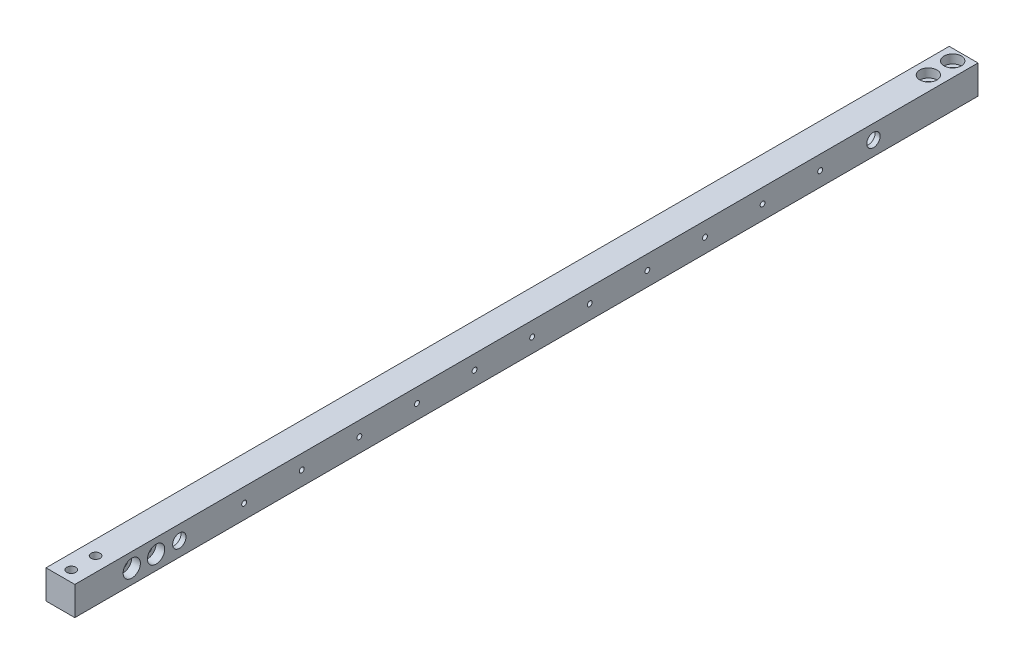
SolidWorks part; units mm, degrees
ref_plane "Front Plane" through (0, 0, 0) normal (0, 0, 1) x (1, 0, 0)
ref_plane "Top Plane" through (0, 0, 0) normal (0, 1, 0) x (1, 0, 0)
ref_plane "Right Plane" through (0, 0, 0) normal (1, 0, 0) x (0, 0, -1)
sketch "Sketch1" plane through (0, 0, 0) normal (0, 0, 1) x (1, 0, 0)
  line L1 (0, 0) -> (15.875, 0)
  line L2 (0, 0) -> (0, 15.875)
  line L3 (0, 15.875) -> (15.875, 15.875)
  line L4 (15.875, 0) -> (15.875, 15.875)
  dimension "D1" = 15.875
  dimension "D2" = 15.875
extrude "Boss-Extrude1" add sketch "Sketch1" along normal blind 497.84
sketch "Sketch8" plane through (0, 0, 0) normal (-1, 0, 0) x (0, 0, 1)
  line L0 (0, 15.875) -> (0, 0) construction
  line L3 (497.84, 0) -> (0, 0) construction
  line L6 (497.84, 15.875) -> (497.84, 0) construction
  circle A0 centre (440.2201, 7.9375) radius 6.8199
  circle A1 centre (57.6199, 7.9375) radius 6.8199
  point P0 (0, 7.9375)
  dimension "D1" = 57.6199
  dimension "D2" = 7.9375
  dimension "D3" = 7.9375
  dimension "D4" = 57.6199
extrude "Cut-Extrude1" cut sketch "Sketch8" against normal blind 13.0861
hole_wizard "L (0.29) Diameter Hole1" positions "Sketch10" profile "Sketch9" hole size "L" standard "ANSI Inch"
sketch "Sketch10" plane through (13.0861, 0, 0) normal (-1, 0, 0) x (0, 0, 1)
  point P0 (57.6199, 7.9375)
  point P3 (440.2201, 7.9375)
sketch "Sketch9" plane through (13.0861, 7.9375, 57.6199) normal (0, 1, 0) x (0, 0, 1)
  line L0 (0, 0) -> (0, 53.013)
  line L1 (0, 53.013) -> (3.683, 50.8)
  line L2 (3.683, 50.8) -> (3.683, 0)
  line L5 (3.683, 0) -> (0, 0)
  line L10 (0, 53.013) -> (-3.683, 50.8) construction
  line L11 (0, -6.35) -> (0, 107.95) construction
  dimension "Hole Dia." = 7.366
  dimension "Hole Depth" = 50.8
  dimension "Drill Angle" = 118
hole_wizard "Tap Drill for #6-32 Tap1" positions "Sketch19" profile "Sketch20" hole size "#6-32" standard "ANSI Inch" end condition through all
sketch "Sketch19" plane through (-468.3125, 1840.2442, -1707.9731) normal (-1, 0, 0) x (0, 0, -1)
  line L0 (-2112.4681, 1832.3067) -> (-1794.9681, 1832.3067) construction
  line L2 (-2205.8131, 1840.2442) -> (-1707.9731, 1840.2442) construction
  point P3 (-2112.4681, 1832.3067)
  point P6 (-2080.7181, 1832.3067)
  point P9 (-2048.9681, 1832.3067)
  point P12 (-2017.2181, 1832.3067)
  point P15 (-1985.4681, 1832.3067)
  point P18 (-1953.7181, 1832.3067)
  point P21 (-1921.9681, 1832.3067)
  point P24 (-1890.2181, 1832.3067)
  point P27 (-1858.4681, 1832.3067)
  point P30 (-1826.7181, 1832.3067)
  point P33 (-1794.9681, 1832.3067)
  dimension "D1" = 7.9375
sketch "Sketch20" plane through (-468.3125, 7.9375, 404.495) normal (0, 1, 0) x (0, 0, 1)
  line L0 (0, 0) -> (0, 484.1875)
  line L1 (0, 484.1875) -> (1.3525, 484.1875)
  line L2 (1.3525, 484.1875) -> (1.3525, 0)
  line L3 (1.3525, 0) -> (0, 0)
  line L4 (0, -6.35) -> (0, 107.95) construction
  dimension "Thru Hole Dia." = 2.7051
  dimension "Thru Hole Depth" = 484.1875
hole_wizard "CBORE for #10 Socket Head Cap Screw3" positions "Sketch21" profile "Sketch22" counterbore size "#10" standard "ANSI Inch"
sketch "Sketch21" plane through (412.8741, 0, -1707.9731) normal (0, -1, 0) x (-1, 0, 0)
  point P0 (871.6616, -2186.4131)
  point P3 (871.6616, -2199.8131)
  point P6 (404.9366, -2186.4131)
  point P9 (404.9366, -2199.8131)
sketch "Sketch22" plane through (-458.7875, 0, 478.44) normal (1, 0, 0) x (0, 0, -1)
  line L0 (0, 0) -> (0, 26.8957)
  line L1 (0, 26.8957) -> (2.4892, 25.4)
  line L2 (2.4892, 25.4) -> (2.4892, 4.826)
  line L3 (2.4892, 4.826) -> (4.7625, 4.826)
  line L4 (4.7625, 4.826) -> (4.7625, 0)
  line L5 (4.7625, 0) -> (0, 0)
  line L6 (0, 26.8957) -> (-2.4892, 25.4) construction
  line L7 (0, -6.35) -> (0, 107.95) construction
  dimension "Hole Dia." = 4.9784
  dimension "Hole Depth" = 25.4
  dimension "C'Bore Dia." = 9.525
  dimension "C'Bore Depth" = 4.826
  dimension "Drill Angle" = 118
hole_wizard "CBORE for #10 Socket Head Cap Screw2" positions "Sketch23" profile "Sketch24" counterbore size "#10" standard "ANSI Inch"
sketch "Sketch23" plane through (412.8741, 15.875, -1707.9731) normal (0, 1, 0) x (1, 0, 0)
  point P0 (-404.9366, -1727.3731)
  point P3 (-404.9366, -1713.9731)
  point P6 (-871.6616, -1727.3731)
  point P9 (-871.6616, -1713.9731)
sketch "Sketch24" plane through (7.9375, 15.875, 19.4) normal (1, 0, 0) x (0, 0, 1)
  line L0 (0, 0) -> (0, 26.8957)
  line L1 (0, 26.8957) -> (2.4892, 25.4)
  line L2 (2.4892, 25.4) -> (2.4892, 4.826)
  line L3 (2.4892, 4.826) -> (4.7625, 4.826)
  line L4 (4.7625, 4.826) -> (4.7625, 0)
  line L5 (4.7625, 0) -> (0, 0)
  line L6 (0, 26.8957) -> (-2.4892, 25.4) construction
  line L7 (0, -6.35) -> (0, 107.95) construction
  dimension "Hole Dia." = 4.9784
  dimension "Hole Depth" = 25.4
  dimension "C'Bore Dia." = 9.525
  dimension "C'Bore Depth" = 4.826
  dimension "Drill Angle" = 118
hole_wizard "CBORE for #10 Socket Head Cap Screw1" positions "Sketch25" profile "Sketch26" counterbore size "#10" standard "ANSI Inch"
sketch "Sketch25" plane through (15.875, 1702.0545, -1707.9731) normal (1, 0, 0) x (0, 0, 1)
  point P0 (2161.0131, 1694.117)
  point P3 (2174.4131, 1694.117)
sketch "Sketch26" plane through (15.875, 7.9375, 453.04) normal (0, 1, 0) x (0, 0, -1)
  line L0 (0, 0) -> (0, 26.8957)
  line L1 (0, 26.8957) -> (2.4892, 25.4)
  line L2 (2.4892, 25.4) -> (2.4892, 4.826)
  line L3 (2.4892, 4.826) -> (4.7625, 4.826)
  line L4 (4.7625, 4.826) -> (4.7625, 0)
  line L5 (4.7625, 0) -> (0, 0)
  line L6 (0, 26.8957) -> (-2.4892, 25.4) construction
  line L7 (0, -6.35) -> (0, 107.95) construction
  dimension "Hole Dia." = 4.9784
  dimension "Hole Depth" = 25.4
  dimension "C'Bore Dia." = 9.525
  dimension "C'Bore Depth" = 4.826
  dimension "Drill Angle" = 118
